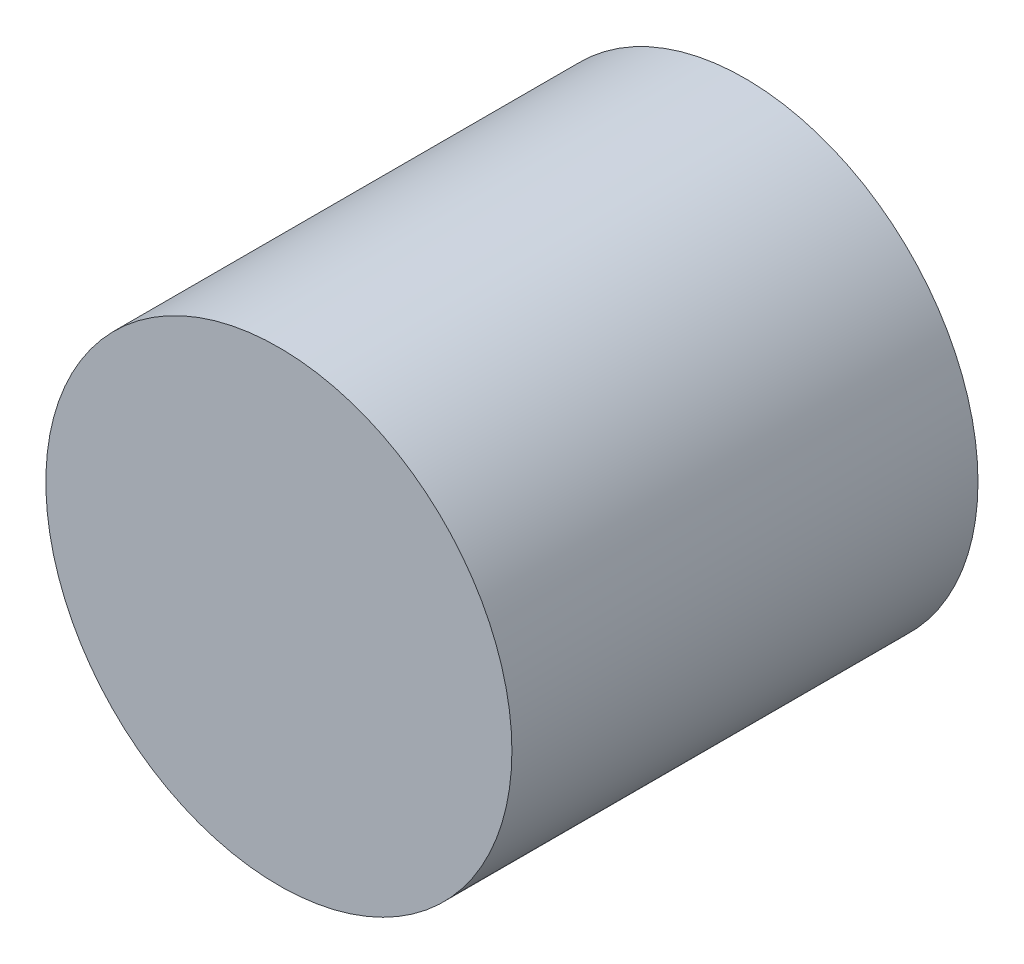
SolidWorks part; units mm, degrees
ref_plane "Front Plane" through (0, 0, 0) normal (0, 0, 1) x (1, 0, 0)
ref_plane "Top Plane" through (0, 0, 0) normal (0, 1, 0) x (1, 0, 0)
ref_plane "Right Plane" through (0, 0, 0) normal (1, 0, 0) x (0, 0, -1)
sketch "Sketch2" plane through (0, 0, 0) normal (0, 0, 1) x (1, 0, 0)
  circle A0 centre (0, 0) radius 5
  dimension "D1" = 10
extrude "Boss-Extrude1" add sketch "Sketch2" along normal blind 10
